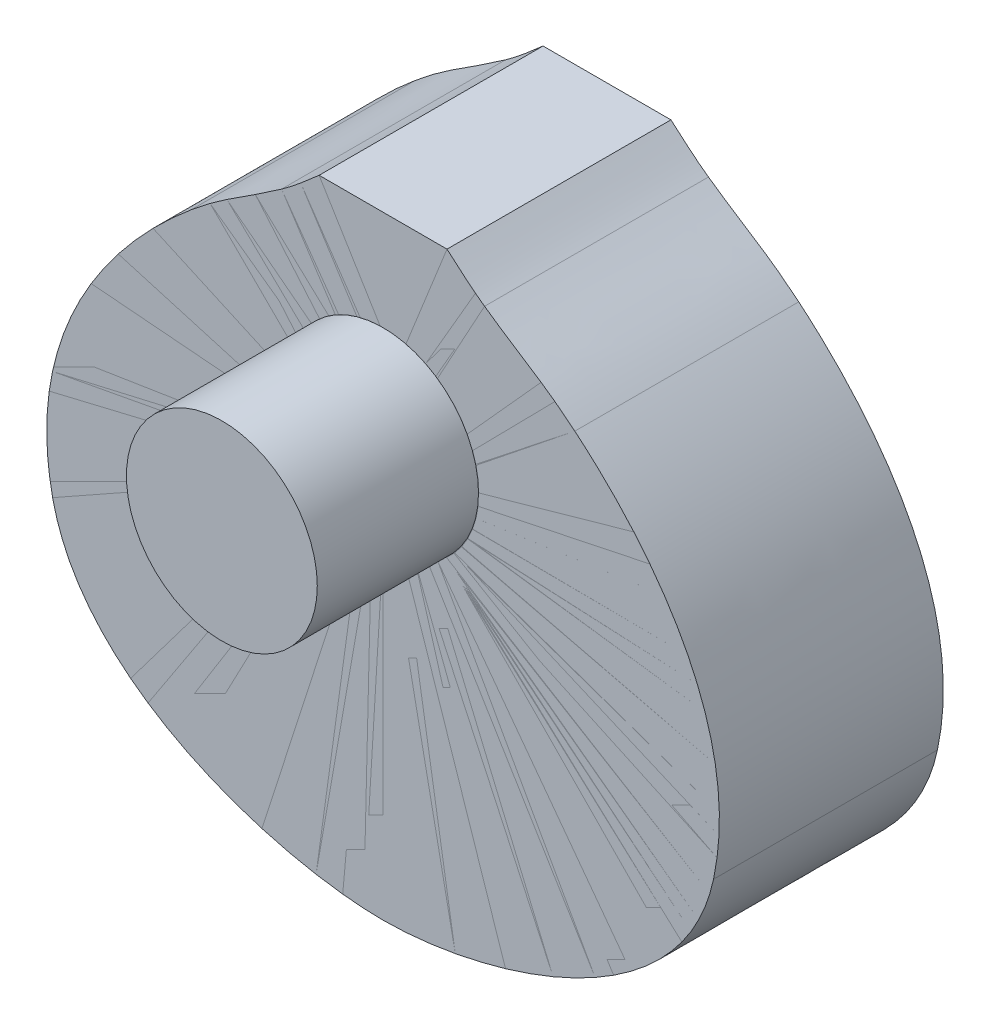
SolidWorks part; units mm, degrees
ref_plane "Alzado" through (0, 0, 0) normal (0, 0, 1) x (1, 0, 0)
ref_plane "Planta" through (0, 0, 0) normal (0, 1, 0) x (1, 0, 0)
ref_plane "Vista lateral" through (0, 0, 0) normal (1, 0, 0) x (0, 0, -1)
sketch "Croquis1" plane through (0, 0, 0) normal (0, 0, 1) x (1, 0, 0)
  line L0 (-28.5608, 136.9164) -> (0, 136.9164)
  line L3 (0, 136.9164) -> (0, -136.9164)
  spline S0 degree 3 poles (-147.5785, -47.2765) (-163.1102, 25.4873) (-105.3607, 78.5809) (-85.6394, 95.0588) knots 0 0 0 0 1 1 1 1
  spline S1 degree 3 poles (-85.6394, 95.0588) (-70.7787, 107.4754) (-62.7858, 110.8395) (-45.3232, 123.1886) knots 0 0 0 0 1 1 1 1
  spline S2 degree 3 poles (-45.3232, 123.1886) (-39.5023, 127.305) (-33.9335, 132.1947) (-28.5608, 136.9164) knots 0 0 0 0 1 1 1 1
  spline S7 degree 3 poles (0, -136.9164) (-46.4413, -136.9164) (-133.8334, -111.6704) (-147.5785, -47.2765) knots 0 0 0 0 1 1 1 1
  dimension "D1" = 273.8328
sketch "Croquis3" plane through (0, 0, 0) normal (0, 0, 1) x (1, 0, 0)
  line L0 (0, 136.9164) -> (0, -136.9164)
  line L1 (0, 136.9164) -> (28.5608, 136.9164)
  spline S0 degree 3 poles (0, -136.9164) (46.4413, -136.9164) (133.8334, -111.6704) (147.5785, -47.2765) knots 0 0 0 0 1 1 1 1
  spline S1 degree 3 poles (147.5785, -47.2765) (163.1102, 25.4873) (105.3607, 78.5809) (85.6394, 95.0588) knots 0 0 0 0 1 1 1 1
  spline S2 degree 3 poles (85.6394, 95.0588) (70.7787, 107.4754) (62.7858, 110.8395) (45.3232, 123.1886) knots 0 0 0 0 1 1 1 1
  spline S3 degree 3 poles (45.3232, 123.1886) (39.5023, 127.305) (33.9335, 132.1947) (28.5608, 136.9164) knots 0 0 0 0 1 1 1 1
extrude "Saliente-Extruir1" add sketch "Croquis1" along normal blind 100
extrude "Saliente-Extruir2" add sketch "Croquis3" along normal blind 100
sketch "Croquis8" plane through (0, 0, 100) normal (0, 0, 1) x (1, 0, 0)
  line L0 (28.5608, 136.9164) -> (-28.5608, 136.9164) construction
  line B0 (0, 6.7699) -> (0, -136.9164)
  line B1 (0, 136.9164) -> (0, 92.3065)
  line B2 (28.5608, 136.9164) -> (0, 136.9164)
  arc B3 (0, 92.3065) -> (0, 6.7699) centre (0, 49.5382) cw
  spline B4 degree 3 poles (0, -136.9164) (46.4413, -136.9164) (133.8334, -111.6704) (147.5785, -47.2765) knots 0 0 0 0 1 1 1 1
  spline B5 degree 3 poles (45.3232, 123.1886) (39.5023, 127.305) (33.9335, 132.1947) (28.5608, 136.9164) knots 0 0 0 0 1 1 1 1
  spline B6 degree 3 poles (85.6394, 95.0588) (70.7787, 107.4754) (62.7858, 110.8395) (45.3232, 123.1886) knots 0 0 0 0 1 1 1 1
  spline B7 degree 3 poles (147.5785, -47.2765) (163.1102, 25.4873) (105.3607, 78.5809) (85.6394, 95.0588) knots 0 0 0 0 1 1 1 1
sketch_block_instance "Bloque4-1"
sketch_block "Bloque4"
surface "Superficie-Plano1" sketch "Croquis8"
sketch "Croquis10" plane through (0, 0, 100) normal (0, 0, 1) x (1, 0, 0)
  line B0 (-28.5608, 136.9164) -> (0, 136.9164)
  line B1 (0, 136.9164) -> (0, 92.3065)
  line B2 (0, 6.7699) -> (0, -136.9164)
  line B3 (0, 6.7699) -> (0, 92.3065) construction
  arc B4 (0, 92.3065) -> (0, 6.7699) centre (0, 49.5382) ccw
  spline B5 degree 3 poles (-147.5785, -47.2765) (-163.1102, 25.4873) (-105.3607, 78.5809) (-85.6394, 95.0588) knots 0 0 0 0 1 1 1 1
  spline B6 degree 3 poles (-85.6394, 95.0588) (-70.7787, 107.4754) (-62.7858, 110.8395) (-45.3232, 123.1886) knots 0 0 0 0 1 1 1 1
  spline B7 degree 3 poles (-45.3232, 123.1886) (-39.5023, 127.305) (-33.9335, 132.1947) (-28.5608, 136.9164) knots 0 0 0 0 1 1 1 1
  spline B8 degree 3 poles (0, -136.9164) (-46.4413, -136.9164) (-133.8334, -111.6704) (-147.5785, -47.2765) knots 0 0 0 0 1 1 1 1
sketch_block_instance "Bloque5-1"
sketch_block "Bloque5"
surface "Superficie-Plano2" sketch "Croquis10"
sketch "Croquis13" plane through (0, 0, 100) normal (0, 0, 1) x (1, 0, 0)
  line L0 (0, 136.9164) -> (0, -136.9164) construction
  circle A0 centre (0, 49.6595) radius 42.6235
  point P0 (0, 92.283)
  point P1 (0, 7.036)
extrude "Saliente-Extruir3" add sketch "Croquis13" along normal blind 72
